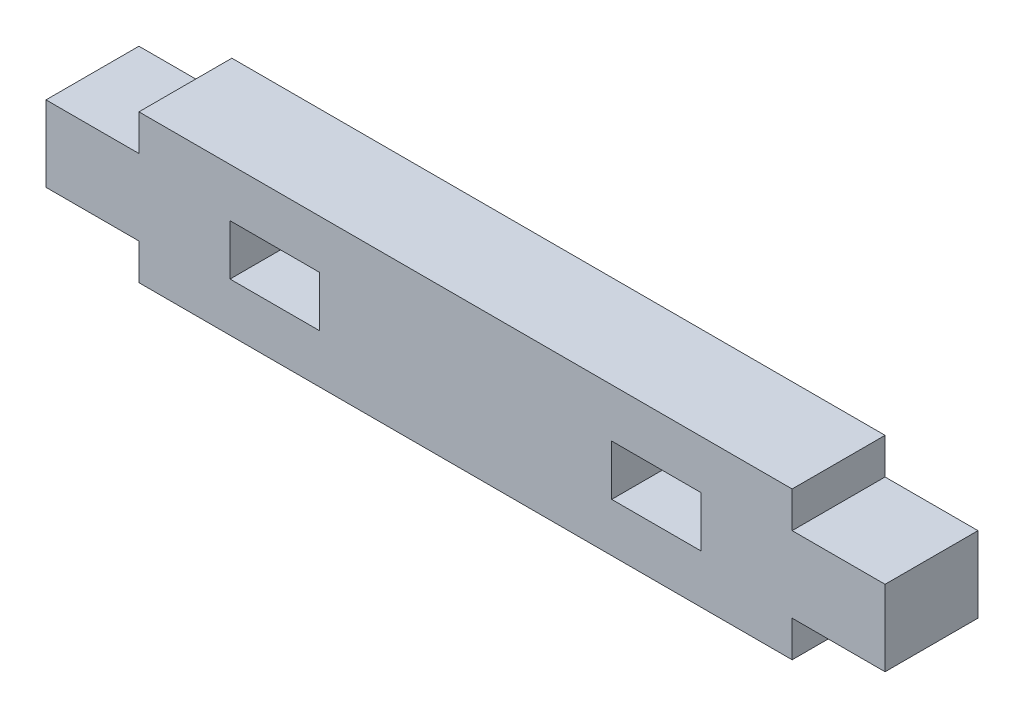
SolidWorks part; units mm, degrees
ref_plane "Front Plane" through (0, 0, 0) normal (0, 0, 1) x (1, 0, 0)
ref_plane "Top Plane" through (0, 0, 0) normal (0, 1, 0) x (1, 0, 0)
ref_plane "Right Plane" through (0, 0, 0) normal (1, 0, 0) x (0, 0, -1)
sketch "Sketch1" plane through (0, 0, 0) normal (0, 0, 1) x (1, 0, 0)
  line L0 (0, 19.9873) -> (0, -14.0711) construction
  line L1 (0, -55) -> (0, 55) construction
  line L2 (-18, 0) -> (0, 0) construction
  line L3 (-18, 8) -> (18, 8) construction
  line L4 (18, 8) -> (18, 6) construction
  line L5 (18, 6) -> (23.15, 6) construction
  line L6 (23.15, 6) -> (23.15, 2) construction
  line L7 (23.15, 2) -> (18, 2) construction
  line L8 (18, 2) -> (18, 0) construction
  line L9 (55, 0) -> (-55, 0) construction
  line L10 (18, 0) -> (0, 0) construction
  line L11 (-18.1, 1.9) -> (-18.1, -0.1)
  line L12 (-18.1, -0.1) -> (0, -0.1)
  line L13 (18.1, -0.1) -> (0, -0.1)
  line L14 (18.1, 1.9) -> (18.1, -0.1)
  line L15 (23.25, 1.9) -> (18.1, 1.9)
  line L16 (23.25, 6.1) -> (23.25, 1.9)
  line L17 (18.1, 6.1) -> (23.25, 6.1)
  line L18 (-18, 2) -> (-18, 0) construction
  line L19 (-23.15, 2) -> (-18, 2) construction
  line L20 (-23.15, 6) -> (-23.15, 2) construction
  line L21 (-18, 6) -> (-23.15, 6) construction
  line L22 (-18, 8) -> (-18, 6) construction
  line L23 (18.1, 8.1) -> (18.1, 6.1)
  line L24 (-18.1, 8.1) -> (18.1, 8.1)
  line L25 (-18.1, 8.1) -> (-18.1, 6.1)
  line L26 (-18.1, 6.1) -> (-23.25, 6.1)
  line L27 (-23.25, 6.1) -> (-23.25, 1.9)
  line L28 (-23.25, 1.9) -> (-18.1, 1.9)
  point P33 (0, 8)
  dimension "D1" = 5.15
  dimension "D2" = 4
  dimension "D3" = 8
  dimension "D4" = 18
  dimension "D5" = 0.1
extrude "Boss-Extrude1" add sketch "Sketch1" along normal blind 5.15
sketch "Sketch2" plane through (0, 0, 5.15) normal (0, 0, 1) x (1, 0, 0)
  line L0 (23.15, 4) -> (0, 4) construction
  line L1 (23.15, 2) -> (23.15, 6) construction
  line L2 (0, -55) -> (0, 55) construction
  line L3 (0, 18.7739) -> (0, -12.3131) construction
  line L4 (8, 5.5) -> (13.15, 5.5) construction
  line L5 (8, 5.5) -> (8, 2.5) construction
  line L6 (8, 2.5) -> (13.15, 2.5) construction
  line L7 (13.15, 5.5) -> (13.15, 2.5) construction
  line L8 (-13.15, 5.5) -> (-13.15, 2.5) construction
  line L9 (-8, 2.5) -> (-13.15, 2.5) construction
  line L10 (-8, 5.5) -> (-8, 2.5) construction
  line L11 (-8, 5.5) -> (-13.15, 5.5) construction
  line L12 (8.1, 5.4) -> (13.05, 5.4)
  line L13 (13.05, 5.4) -> (13.05, 2.6)
  line L14 (8.1, 2.6) -> (13.05, 2.6)
  line L15 (8.1, 5.4) -> (8.1, 2.6)
  line L16 (-13.05, 5.4) -> (-13.05, 2.6)
  line L17 (-8.1, 2.6) -> (-13.05, 2.6)
  line L18 (-8.1, 5.4) -> (-8.1, 2.6)
  line L19 (-8.1, 5.4) -> (-13.05, 5.4)
  line L20 (23.15, 3.9) -> (0, 3.9)
  line L21 (0.1, 18.7739) -> (0.1, -12.3131)
  point P10 (8, 4)
  dimension "D1" = 8
  dimension "D2" = 5.15
  dimension "D3" = 3
  dimension "D4" = 0.1
extrude "Cut-Extrude1" cut sketch "Sketch2" against normal through all contours L18 L19 L16 L17 | L12 L13 L14 L15
